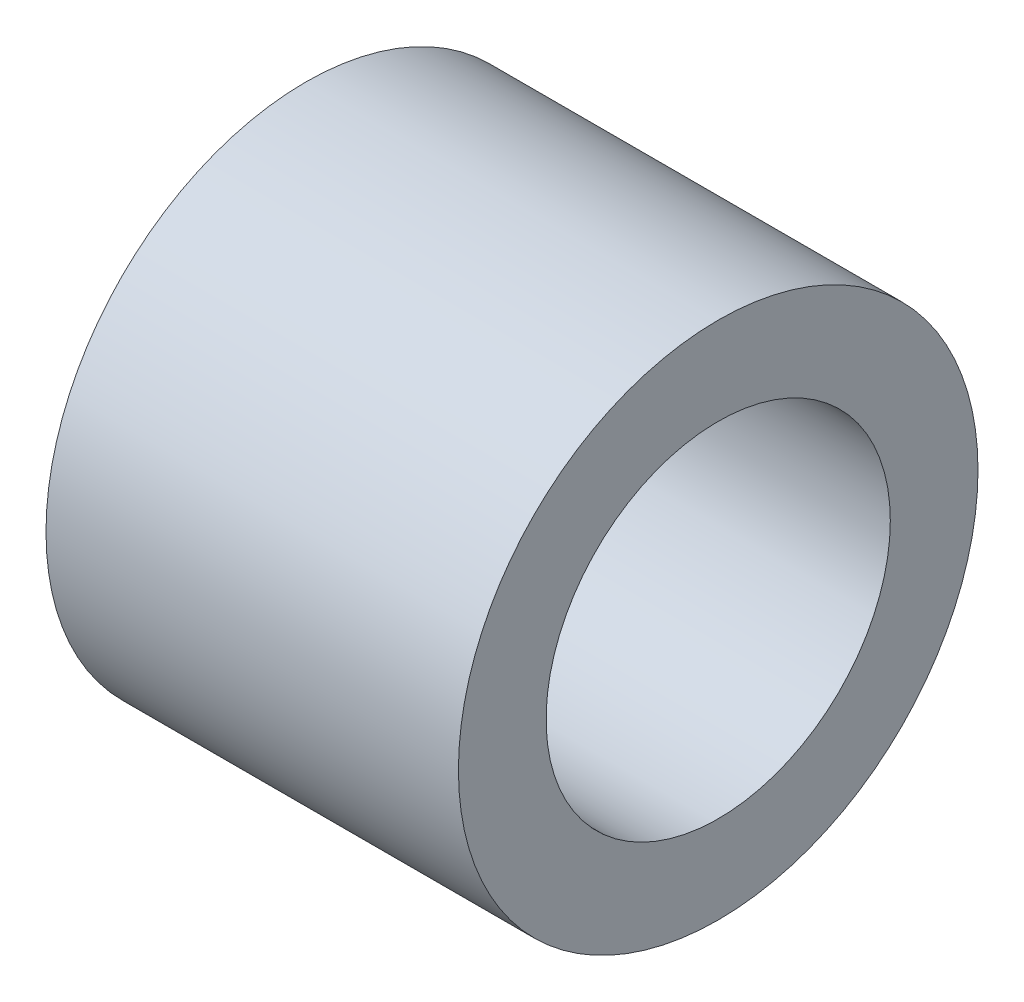
SolidWorks part; units mm, degrees
ref_plane "Front Plane" through (0, 0, 0) normal (0, 0, 1) x (1, 0, 0)
ref_plane "Top Plane" through (0, 0, 0) normal (0, 1, 0) x (1, 0, 0)
ref_plane "Right Plane" through (0, 0, 0) normal (1, 0, 0) x (0, 0, -1)
sketch "Sketch1" plane through (0, 0, 0) normal (1, 0, 0) x (0, 0, -1)
  circle A0 centre (0, 0) radius 2.65
  circle A1 centre (0, 0) radius 4
  dimension "D1" = 5.3
  dimension "D2" = 8
extrude "Boss-Extrude1" add sketch "Sketch1" along normal blind 6.35
